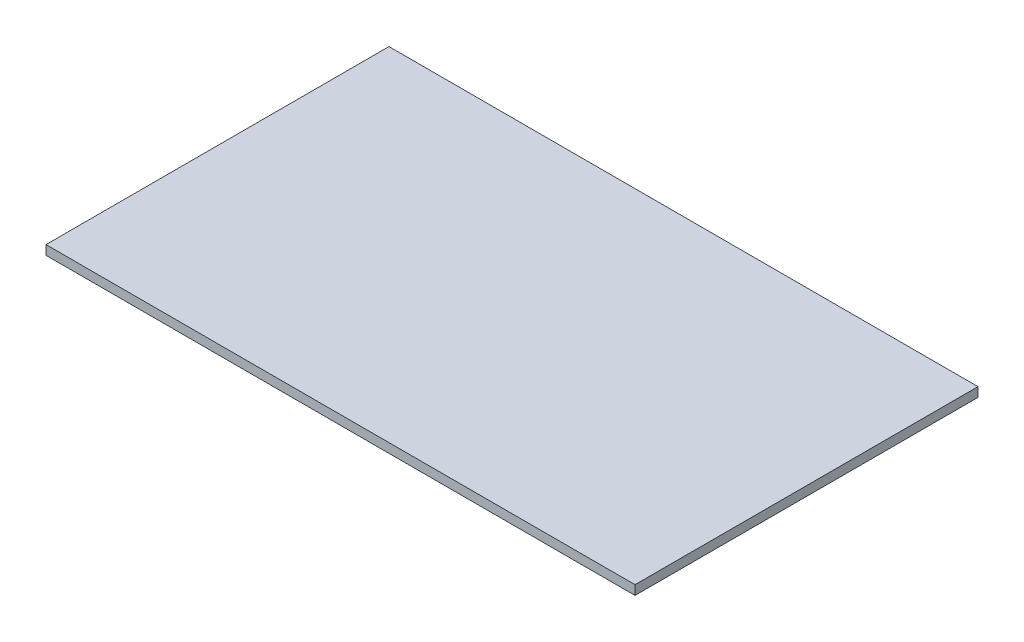
SolidWorks part; units mm, degrees
ref_plane "Front Plane" through (0, 0, 0) normal (0, 0, 1) x (1, 0, 0)
ref_plane "Top Plane" through (0, 0, 0) normal (0, 1, 0) x (1, 0, 0)
ref_plane "Right Plane" through (0, 0, 0) normal (1, 0, 0) x (0, 0, -1)
sketch "Sketch1" plane through (0, 0, 0) normal (0, 1, 0) x (1, 0, 0)
  line L1 (50.165, 29.21) -> (-50.165, 29.21)
  line L2 (50.165, 29.21) -> (50.165, -29.21)
  line L3 (50.165, -29.21) -> (-50.165, -29.21)
  line L4 (-50.165, 29.21) -> (-50.165, -29.21)
  line L5 (50.165, 29.21) -> (-50.165, -29.21) construction
  line L6 (50.165, -29.21) -> (-50.165, 29.21) construction
  point P0 (0, 0)
  dimension "D1" = 100.33
  dimension "D2" = 58.42
extrude "Boss-Extrude1" add sketch "Sketch1" along normal blind 1.5875
